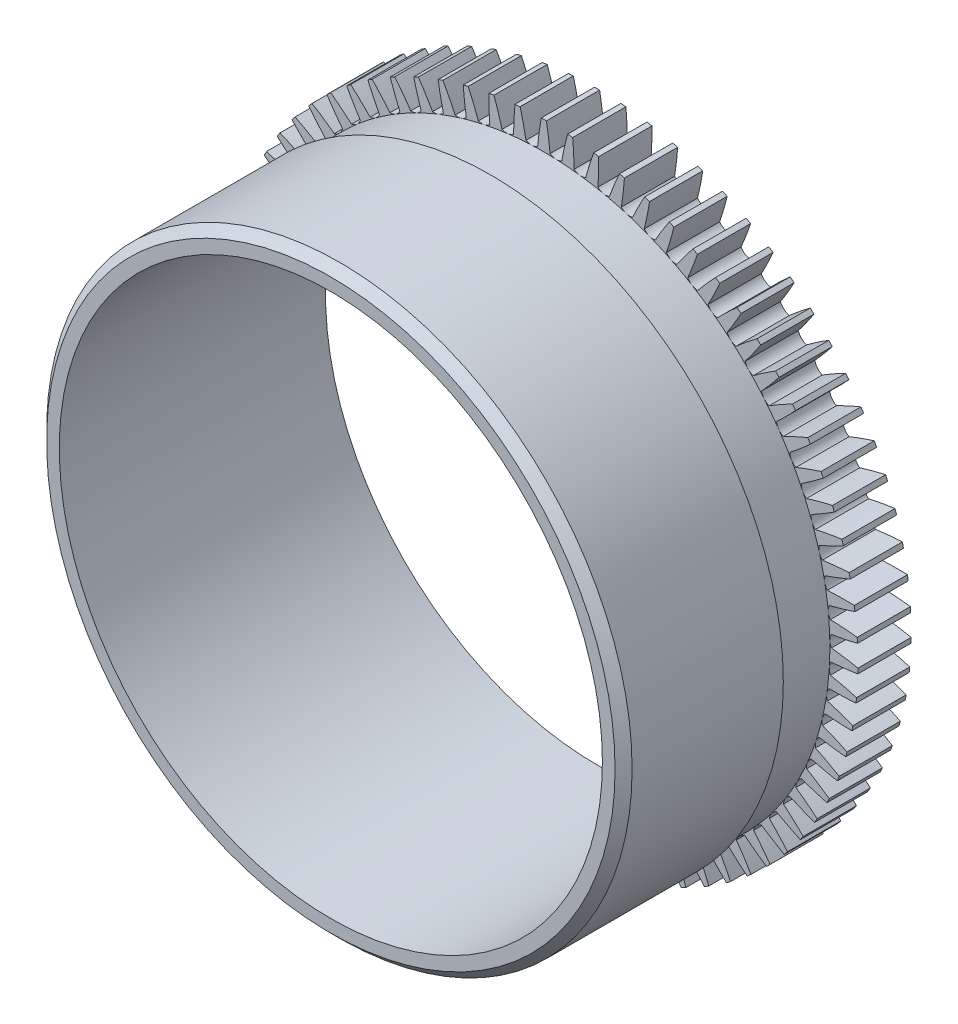
SolidWorks part; units mm, degrees
ref_plane "Plan de face" through (0, 0, 0) normal (0, 0, 1) x (1, 0, 0)
ref_plane "Plan de dessus" through (0, 0, 0) normal (0, 1, 0) x (1, 0, 0)
ref_plane "Plan de droite" through (0, 0, 0) normal (1, 0, 0) x (0, 0, -1)
sketch "Esquisse1" plane through (0, 0, 0) normal (0, 0, 1) x (1, 0, 0)
  circle A0 centre (0, 0) radius 25.5
  circle A1 centre (0, 0) radius 29.5
  dimension "D1" = 51
  dimension "D2" = 4
extrude "Boss.-Extru.1" add sketch "Esquisse1" along normal blind 5
sketch3d "Esquisse3D3" plane through (0, 0, 0) normal (0, 0, 1) x (1, 0, 0)
  dimension "D1" = 5
sketch "Esquisse3" plane through (0, 0, 5) normal (0, 0, -1) x (-1, 0, 0)
  line L5 (0, 0) -> (0, -58.6608) construction
  line L6 (1, -31.5) -> (-1, -31.5)
  line L7 (-1, -31.5) -> (-1, -29.5)
  line L8 (1, -31.5) -> (1, -29.5)
  arc A2 (-0.55, -27) -> (0.55, -27) centre (0, -27.9869) cw
  arc A3 (-1, -29.5) -> (-0.55, -27) centre (-30.274, -22.9402) ccw
  arc A4 (1, -29.5) -> (0.55, -27) centre (30.274, -22.9402) cw
  dimension "D1" = 29.5
  dimension "D2" = 1.1
  dimension "D4" = 30
  dimension "D3" = 2
  dimension "D5" = 2.5
  dimension "D7" = 2
extrude "Enlèv. mat.-Extru.1" cut sketch "Esquisse3" against normal through all and the other way through all
pattern_circular "Répétition circulaire1" count 75 over 360 about axis through (0, 0, 0) along (0, 0, 1) of "Enlèv. mat.-Extru.1"
sketch "Esquisse4" plane through (0, 0, 5) normal (0, 0, 1) x (1, 0, 0)
  circle A0 centre (0, 0) radius 26.8571
  circle A1 centre (0, 0) radius 25.5
extrude "Boss.-Extru.2" add sketch "Esquisse4" along normal blind 5
sketch "Esquisse5" plane through (0, 0, 10) normal (0, 0, 1) x (1, 0, 0)
  circle A0 centre (0, 0) radius 27.49
  circle A1 centre (0, 0) radius 25.5
  dimension "D1" = 54.98
extrude "Boss.-Extru.3" add sketch "Esquisse5" along normal blind 15
chamfer "Chanfrein1" distance 0.8 angle 45 1 edges at (27.49, 0, 25)
